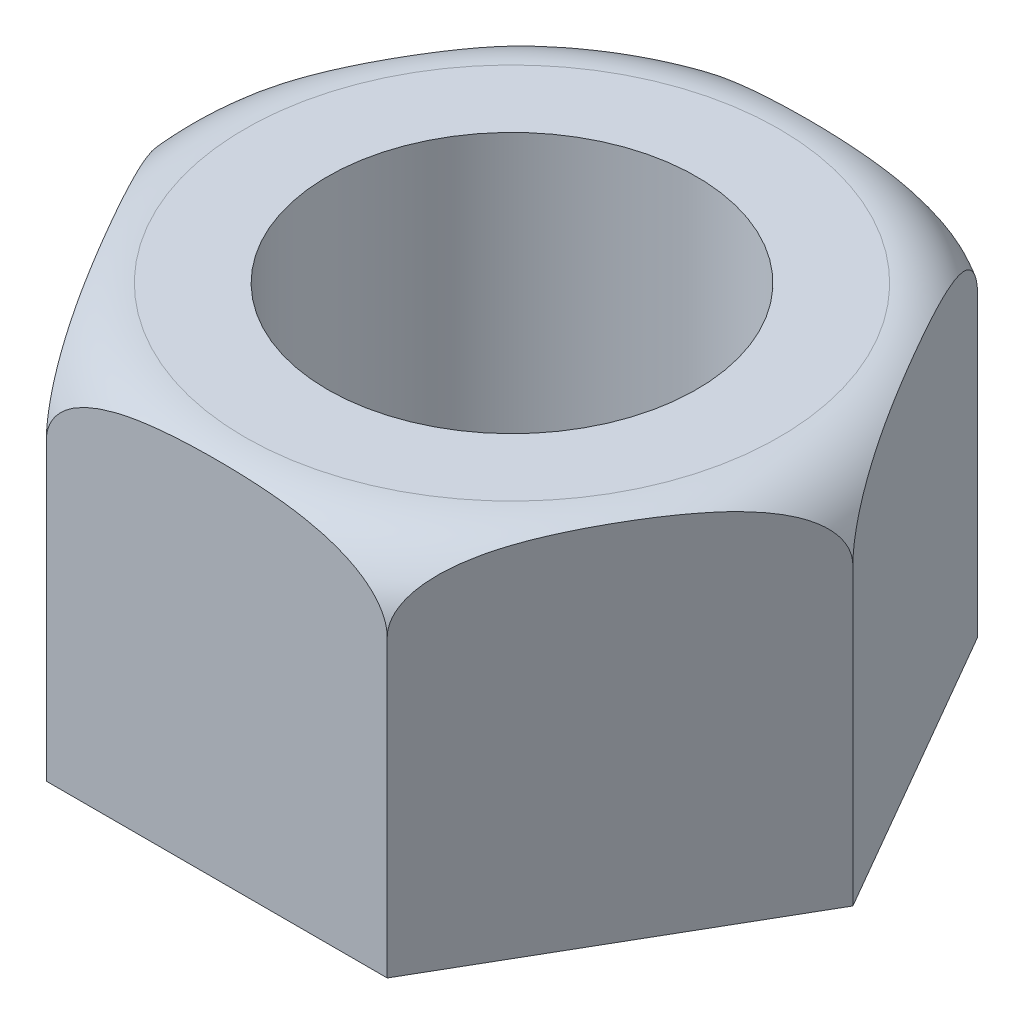
SolidWorks part; units mm, degrees
ref_plane "Front Plane" through (0, 0, 0) normal (0, 0, 1) x (1, 0, 0)
ref_plane "Top Plane" through (0, 0, 0) normal (0, 1, 0) x (1, 0, 0)
ref_plane "Right Plane" through (0, 0, 0) normal (1, 0, 0) x (0, 0, -1)
sketch "Sketch1" plane through (0, 0, 0) normal (0, 1, 0) x (1, 0, 0)
  line L1 (9.2376, 0) -> (4.6188, 8)
  line L2 (4.6188, 8) -> (-4.6188, 8)
  line L3 (-4.6188, 8) -> (-9.2376, 0)
  line L4 (-9.2376, 0) -> (-4.6188, -8)
  line L5 (-4.6188, -8) -> (4.6188, -8)
  line L6 (4.6188, -8) -> (9.2376, 0)
  circle A0 centre (0, 0) radius 8 construction
  circle A1 centre (0, 0) radius 5
  dimension "D2" = 10
  dimension "D1" = 16
extrude "Boss-Extrude1" add sketch "Sketch1" along normal blind 10
sketch "Sketch2" plane through (0, 0, 0) normal (0, 0, 1) x (1, 0, 0)
  line L0 (9.2376, 10) -> (7.2376, 10)
  line L1 (-4.6188, 10) -> (4.6188, 10) construction
  line L2 (9.2376, 8) -> (9.2376, 10)
  line L3 (9.2376, 10) -> (9.2376, 0) construction
  line L4 (0, 0) -> (0, 2.62) construction
  arc A0 (9.2376, 8) -> (7.2376, 10) centre (7.2376, 8) ccw
  point P10 (9.2376, 10)
  dimension "D1" = 2
revolve "Cut-Revolve1" cut sketch "Sketch2" angle 360 about L4
